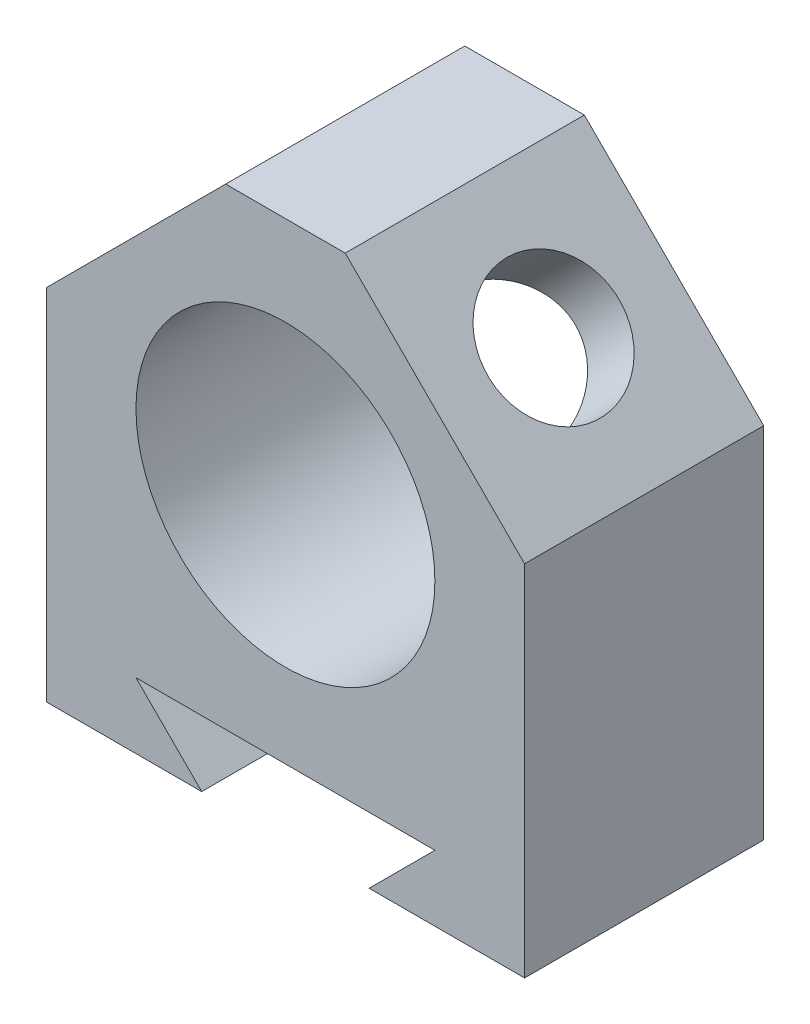
SolidWorks part; units mm, degrees
material "Cast Carbon Steel"
ref_plane "Front Plane" through (0, 0, 0) normal (0, 0, 1) x (1, 0, 0)
ref_plane "Top Plane" through (0, 0, 0) normal (0, 1, 0) x (1, 0, 0)
ref_plane "Right Plane" through (0, 0, 0) normal (1, 0, 0) x (0, 0, -1)
sketch "Sketch1" plane through (0, 0, 0) normal (0, 0, 1) x (1, 0, 0)
  line L0 (25, 0) -> (-25, 0)
  line L1 (-25, 0) -> (-14, -11)
  line L2 (-14, -11) -> (-40, -11)
  line L3 (-40, -11) -> (-40, 49)
  line L5 (0, 79) -> (10, 79)
  line L6 (0, 79) -> (0, 64)
  line L7 (0, 14) -> (0, 0)
  line L8 (0, 79) -> (0, 0) construction
  line L9 (40, 49) -> (10, 79)
  line L10 (40, -11) -> (40, 49)
  line L11 (14, -11) -> (40, -11)
  line L12 (25, 0) -> (14, -11)
  line L13 (-40, 49) -> (-10, 79)
  line L14 (0, 79) -> (-10, 79)
  circle A0 centre (0, 39) radius 25
  dimension "D5" = 50
  dimension "D1" = 26
  dimension "D2" = 80
  dimension "D3" = 11
  dimension "D4" = 45
  dimension "D6" = 50
  dimension "D7" = 60
  dimension "D8" = 90
  dimension "D9" = 45
  dimension "D10" = 45
extrude "Boss-Extrude1" add sketch "Sketch1" against normal blind 40
sketch "Sketch2" plane through (44.5, 44.5, 0) normal (0.7071, 0.7071, 0) x (0, 0, -1)
  line L0 (40, 48.7904) -> (0, 48.7904) construction
  line L2 (40, 6.364) -> (40, 48.7904) construction
  circle A0 centre (20, 27.7904) radius 11
  dimension "D3" = 22
  dimension "D1" = 21
  dimension "D2" = 20
extrude "Cut-Extrude1" cut sketch "Sketch2" against normal up to next
sketch "Sketch3" plane through (-44.5, 44.5, 0) normal (-0.7071, 0.7071, 0) x (0, 0, 1)
  line L0 (-40, 48.7904) -> (0, 48.7904) construction
  line L1 (-8.453, 27.7904) -> (-14.2265, 37.7904)
  line L2 (-14.2265, 37.7904) -> (-25.7735, 37.7904)
  line L3 (-25.7735, 37.7904) -> (-31.547, 27.7904)
  line L4 (-31.547, 27.7904) -> (-25.7735, 17.7904)
  line L5 (-25.7735, 17.7904) -> (-14.2265, 17.7904)
  line L6 (-14.2265, 17.7904) -> (-8.453, 27.7904)
  line L7 (0, 6.364) -> (0, 48.7904) construction
  circle A0 centre (-20, 27.7904) radius 10 construction
  dimension "D1" = 20
  dimension "D2" = 21
  dimension "D3" = 20
  dimension "D4" = 10
extrude "Cut-Extrude3" cut sketch "Sketch3" against normal up to next
